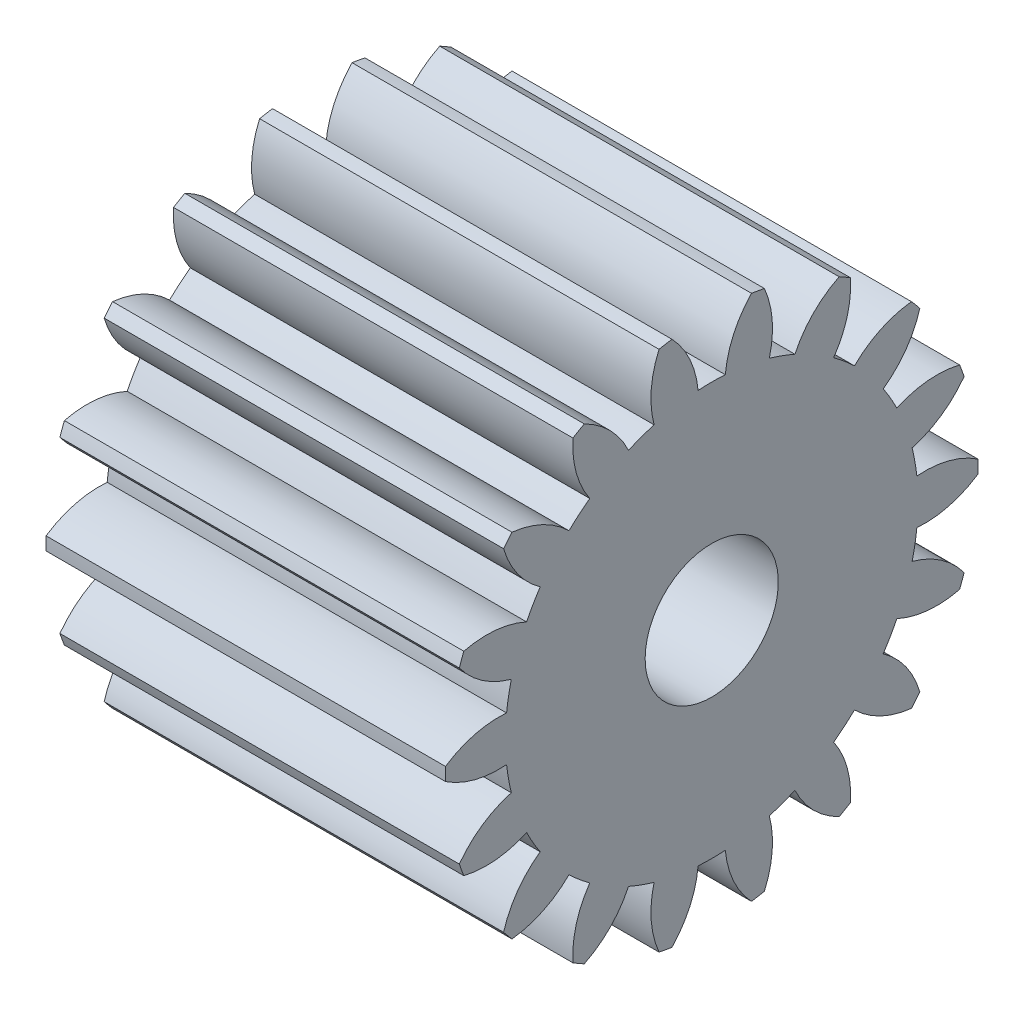
SolidWorks part; units mm, degrees
ref_plane "Plane1" through (0, 0, 0) normal (0, 0, 1) x (1, 0, 0)
ref_plane "Plane2" through (0, 0, 0) normal (0, 1, 0) x (1, 0, 0)
ref_plane "Plane3" through (0, 0, 0) normal (1, 0, 0) x (0, 0, -1)
sketch "HoldingSke" plane through (0, 0, 0) normal (0, 1, 0) x (1, 0, 0)
  line L0 (0, 0) -> (0.9511, -0.309)
  line L1 (-15, 0) -> (100, 0) construction
  line L2 (0, 0) -> (-2.1039, 2.3779)
  line L3 (0, 0) -> (-11.863, 4.5341)
  line L4 (0, 0) -> (8.2133, 2.6687)
  line L5 (0, 0) -> (46.8476, 17.4728)
  line L6 (0, 0) -> (-12.4344, -8.3896)
  line L7 (-2.1039, 2.3779) -> (8.6586, 51.2059)
  line L8 (-76.2, 54.61) -> (-75.3, 54.61)
  line L9 (-71.009, 38.7566) -> (-53.1078, 45.2721)
  line L10 (-76.2, 71.12) -> (104.1128, 71.12)
  line L11 (0, 0) -> (-15, 0)
  line L12 (-76.2, 101.6) -> (-76.162, 101.6)
  line L13 (24.9733, 27.94) -> (52.9518, 28.4284)
  line L14 (24.9733, 27.94) -> (24.9743, 27.94)
  line L15 (24.9733, 27.94) -> (100.4006, 29.5858)
  line L16 (-63.627, -1) -> (-12.827, -1)
  circle A0 centre (0, 0) radius 2.5
  circle A1 centre (0, 0) radius 7.749
  circle A2 centre (0, 0) radius 37.5
  circle A3 centre (0, 0) radius 2.5
  dimension "MHD" = 15.498
  dimension "Hub_dia" = 75
  dimension "Bore" = 5
  dimension "MBD" = 5
  dimension "Num_teeth" = 18
  dimension "Pitch" = 1
  dimension "Overall_len" = 50
  dimension "Show_teeth" = 18
  dimension "Thickness" = 15
  dimension "OAL" = 50.0001
  dimension "T_dim" = 0.9
  dimension "Ap" = 20
  dimension "H" = 19.05
  dimension "Pitch_radius" = 180.3128
  dimension "Width" = 15
  dimension "Backlash" = 0.038
  dimension "Addendum_fac" = 1
  dimension "Dedendum_fac" = 1.25
  dimension "Clearance_fac" = 0.25
  dimension "Dedendum_add" = 0.001
  dimension "Module" = 1
sketch "BasProSke" plane through (0, 0, 0) normal (0, 1, 0) x (1, 0, 0)
  line L0 (-10, 0) -> (60, 0) construction
  line L1 (0, 0) -> (0, 10)
  line L2 (0, 0) -> (15, 0)
  line L3 (15, 0) -> (15, 10)
  line L4 (15, 10) -> (0, 10)
  dimension "Thickness" = 15
  dimension "Diameter" = 20
revolve "Base-Revolve" add sketch "BasProSke" angle 360 about L0
sketch "TooCutSke" plane through (0, 0, 0) normal (1, 0, 0) x (0, 0, -1)
  line L1 (0, 0) -> (0, 107) construction
  line L2 (0, 0) -> (-0.8509, 8.9597) construction
  line L3 (0, 0) -> (-3.1157, 17.6701) construction
  line L4 (-0.8509, 8.9597) -> (-1.5579, 8.835) construction
  arc A0 (0.5106, 7.7322) -> (-0.5106, 7.7322) centre (0, 0) ccw
  arc A1 (1.5152, 9.9102) -> (-1.5152, 9.9102) centre (0, 0) ccw
  circle A2 centre (0, 0) radius 9 construction
  circle A3 centre (0, 0) radius 8.4572 construction
  arc A4 (-0.5106, 7.7322) -> (-1.5152, 9.9102) centre (-4.0952, 7.3996) ccw
  arc A5 (1.5152, 9.9102) -> (0.5106, 7.7322) centre (4.0952, 7.3996) ccw
  dimension "Root_dia" = 15.498
  dimension "Overcut_dia" = 20.0508
  dimension "Pitch_dia" = 18
  dimension "Base_dia" = 16.9145
  dimension "Flank_rad" = 3.6
  dimension "Half_ang" = 10
  dimension "Half_CT" = 0.7179
extrude "ToothCut" cut sketch "TooCutSke" along normal through all
fillet "Breaks" [suppressed] radius 0.02
fillet "RootFillets" [suppressed] radius 0.251
pattern_circular "TeethCuts" count 18 every 20 about axis through (-10, 0, 0) along (1, 0, 0) of "ToothCut", "RootFillets", "Breaks"
sketch "HubNeaOneSke" plane through (0, 0, 0) normal (-1, 0, 0) x (0, 0, 1)
  circle A0 centre (0, 0) radius 7.749
  dimension "Diameter" = 15.498
extrude "HubNearOne" [suppressed] add sketch "HubNeaOneSke" along normal blind 35.0001
sketch "HubNeaBotSke" plane through (0, 0, 0) normal (-1, 0, 0) x (0, 0, 1)
  circle A0 centre (0, 0) radius 7.749
  dimension "Diameter" = 15.498
extrude "HubNearBoth" [suppressed] add sketch "HubNeaBotSke" along normal blind 17.5
ref_plane "FarPln" through (15, 0, 0) normal (1, 0, 0) x (0, 0, -1)
sketch "HubFarSke" plane through (15, 0, 0) normal (1, 0, 0) x (0, 0, -1)
  circle A0 centre (0, 0) radius 7.749
  dimension "Diameter" = 15.498
extrude "HubFar" [suppressed] add sketch "HubFarSke" along normal blind 17.5
sketch "BorSke" plane through (0, 0, 0) normal (1, 0, 0) x (0, 0, -1)
  circle A0 centre (0, 0) radius 2.5
  dimension "Diameter" = 5
extrude "Bore" cut sketch "BorSke" along normal mid plane 100.0001
sketch "KeySke" plane through (0, 0, 0) normal (1, 0, 0) x (0, 0, -1)
  line L0 (-1, 0) -> (-1, 3.4)
  line L1 (-1, 3.4) -> (1, 3.4)
  line L2 (1, 3.4) -> (1, 0)
  line L3 (0, 0) -> (0, 34) construction
  line L4 (-1, 0) -> (1, 0)
  dimension "Offset" = 3.4
  dimension "Width" = 2
extrude "Keyway" [suppressed] cut sketch "KeySke" along normal mid plane 100.0001
pattern_circular "Keyway2" [suppressed] count 2 every 90 about axis through (-10, 0, 0) along (1, 0, 0)
equation "' \"Module@HoldingSke\" = 6.35"
equation "' \"Num_teeth@HoldingSke\" = 12"
equation "' \"Ap@HoldingSke\" =  20"
equation "' \"Ap@HoldingSke\" = 20"
equation "' \"Width@HoldingSke\" = 0.5 * 25.4"
equation "' \"Hub_dia@HoldingSke\"= 1 * 25.4"
equation "' \"Hub_dia@HoldingSke\" = 1 * 25.4"
equation "' \"Overall_len@HoldingSke\" = 1.0 * 25.4"
equation "' \"Bore@HoldingSke\" = 0.75 * 25.4"
equation "' \"T_dim@HoldingSke\" = 0.1 * 25.4"
equation "' \"Width@KeySke\" = 0.25 * 25.4"
equation "' \"Show_teeth@HoldingSke\" = 13"
equation "' \"Backlash@HoldingSke\" = 0.009 * 25.4"
equation "' \"Addendum_fac@HoldingSke\" = 1.0"
equation "' \"Dedendum_fac@HoldingSke\" = 1.25"
equation "' \"Dedendum_add@HoldingSke\" = 0.00005 * 25.4"
equation "' \"Clearance_fac@HoldingSke\" = 0.25"
equation "\"Pitch@HoldingSke\" = 1 / \"Module@HoldingSke\""
equation "\"Overcut_dia@TooCutSke\" = (\"Num_teeth@HoldingSke\" + 2 * \"Addendum_fac@HoldingSke\") / \"Pitch@HoldingSke\" + 0.002 * 25.4"
equation "\"Pitch_dia@TooCutSke\" = \"Num_teeth@HoldingSke\" / \"Pitch@HoldingSke\""
equation "\"Base_dia@TooCutSke\" = \"Num_teeth@HoldingSke\" / \"Pitch@HoldingSke\" * cos((\"Ap@HoldingSke\"  * 3.14159265 / 180))"
equation "\"Root_dia@TooCutSke\" = (\"Num_teeth@HoldingSke\" + 2) / \"Pitch@HoldingSke\" - 2 * (\"Addendum_fac@HoldingSke\" + \"Dedendum_fac@HoldingSke\") / \"Pitch@HoldingSke\" - \"Dedendum_add@HoldingSke\" * 2"
equation "\"Half_ang@TooCutSke\" = 180 / \"Num_teeth@HoldingSke\""
equation "\"Half_CT@TooCutSke\" = \"Num_teeth@HoldingSke\" / \"Pitch@HoldingSke\" * sin((3.14159265 / 2 / \"Num_teeth@HoldingSke\")) / 2 - 7 * \"Backlash@HoldingSke\" / 4"
equation "\"Flank_rad@TooCutSke\" = \"Num_teeth@HoldingSke\" / \"Pitch@HoldingSke\" / 5"
equation "\"Radius@RootFillets\" = \"Clearance_fac@HoldingSke\" / \"Pitch@HoldingSke\" + \"Dedendum_add@HoldingSke\""
equation "\"Break_rad@Breaks\" = 0.02 / \"Pitch@HoldingSke\""
equation "\"Thickness@HoldingSke\" = \"Width@HoldingSke\""
equation "\"OAL@HoldingSke\" = \"Thickness@HoldingSke\""
equation "\"MHD@HoldingSke\" = (\"Num_teeth@HoldingSke\" + 2) / \"Pitch@HoldingSke\" - 2 * (\"Addendum_fac@HoldingSke\" + \"Dedendum_fac@HoldingSke\")  / \"Pitch@HoldingSke\" - \"Dedendum_add@HoldingSke\" * 2"
equation "\"MBD@HoldingSke\" = (\"Num_teeth@HoldingSke\" + 2) / \"Pitch@HoldingSke\" - 2 * (\"Addendum_fac@HoldingSke\" + \"Dedendum_fac@HoldingSke\")  / \"Pitch@HoldingSke\" - \"Dedendum_add@HoldingSke\" * 2 - 0.002 * 25.4"
equation "\"MHD@HoldingSke\" = ((sgn( \"MHD@HoldingSke\" - \"Hub_dia@HoldingSke\" )-1)*( \"MHD@HoldingSke\" - \"Hub_dia@HoldingSke\" ))/-2+ \"Hub_dia@HoldingSke\""
equation "\"MBD@HoldingSke\" = ((sgn( \"MBD@HoldingSke\" - \"Bore@HoldingSke\" )-1)*( \"MBD@HoldingSke\" - \"Bore@HoldingSke\" ))/-2+ \"Bore@HoldingSke\""
equation "\"OAL@HoldingSke\" = ((sgn( \"OAL@HoldingSke\" - \"Overall_len@HoldingSke\" )+1)*( \"OAL@HoldingSke\" - \"Overall_len@HoldingSke\" ))/2 + \"Overall_len@HoldingSke\" + 0.000002 * 25.4"
equation "\"Num_teeth@TeethCuts\" = int( \"Show_teeth@HoldingSke\" ) + 1"
equation "\"Num_teeth@TeethCuts\" = ((sgn( \"Num_teeth@TeethCuts\" - \"Num_teeth@HoldingSke\" )-1)*( \"Num_teeth@TeethCuts\" - \"Num_teeth@HoldingSke\" ))/-2+ \"Num_teeth@HoldingSke\""
equation "\"Num_teeth@TeethCuts\" = ((sgn( \"Num_teeth@TeethCuts\" - 2.0)+1)*( \"Num_teeth@TeethCuts\" - 2.0))/2 +2.0"
equation "\"Angle@TeethCuts\" = 360.0 / \"Num_teeth@HoldingSke\""
equation "\"Diameter@BasProSke\" = (\"Num_teeth@HoldingSke\" + 2 * \"Addendum_fac@HoldingSke\") / \"Pitch@HoldingSke\""
equation "\"Thickness@BasProSke\"  = \"Thickness@HoldingSke\""
equation "' \"Fillet_rad@BasProSke\" =  \"Thickness@HoldingSke\" * 0.05"
equation "' \"Fillet_rad@BasProSke\" = \"Thickness@HoldingSke\" * 0.05"
equation "\"MHD@HoldingSke\" = ((sgn( \"MHD@HoldingSke\" - \"Root_dia@TooCutSke\" )-1)*( \"MHD@HoldingSke\" - \"Root_dia@TooCutSke\" ))/-2+ \"Root_dia@TooCutSke\""
equation "\"Diameter@HubNeaOneSke\" = \"MHD@HoldingSke\""
equation "\"Length@HubNearOne\" = \"OAL@HoldingSke\" - \"Thickness@BasProSke\""
equation "\"Diameter@HubNeaBotSke\" = \"MHD@HoldingSke\""
equation "\"Length@HubNearBoth\" = ( \"OAL@HoldingSke\" - \"Thickness@BasProSke\" ) / 2.0"
equation "\"Thickness@FarPln\" = \"Thickness@BasProSke\""
equation "\"Diameter@HubFarSke\" = \"MHD@HoldingSke\""
equation "\"Length@HubFar\" = ( \"OAL@HoldingSke\" - \"Thickness@BasProSke\" ) / 2.0"
equation "\"Diameter@BorSke\" = \"MBD@HoldingSke\""
equation "\"D1@Bore\" = \"OAL@HoldingSke\" * 2.0"
equation "\"D1@Keyway\" = \"OAL@HoldingSke\" * 2.0"
equation "\"Offset@KeySke\" = \"T_dim@HoldingSke\" + \"MBD@HoldingSke\" / 2.0"
